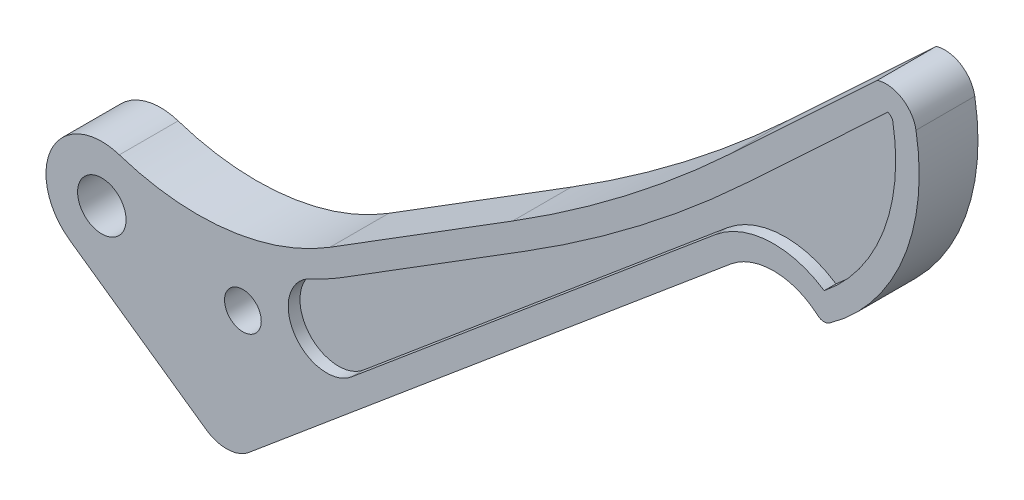
SolidWorks part; units mm, degrees
material "6061 Alloy"
ref_plane "Front Plane" through (0, 0, 0) normal (0, 0, 1) x (1, 0, 0)
ref_plane "Top Plane" through (0, 0, 0) normal (0, 1, 0) x (1, 0, 0)
ref_plane "Right Plane" through (0, 0, 0) normal (1, 0, 0) x (0, 0, -1)
sketch "Sketch1" plane through (0, 0, 0) normal (0, 0, 1) x (1, 0, 0)
  line L0 (36.4205, -14.9567) -> (38.1, -14.9567)
  line L1 (36.446, -14.812) -> (36.4205, -14.9567) construction
  line L2 (39.3098, -38.1358) -> (169.8026, 71.3084)
  line L3 (38.1, -5.4317) -> (37.2385, -10.3173) construction
  line L4 (38.1, -5.4317) -> (38.1, -27.0885) construction
  line L5 (28.2156, -38.2409) -> (-8.6667, -12.3423)
  line L6 (61.6023, 21.14) -> (110.9172, 51.9322)
  line L7 (209.4421, 134.1065) -> (169.8026, 97.1168)
  arc A0 (4.7355, 14.3185) -> (-8.6667, -12.3423) centre (0, 0) ccw
  arc A1 (36.446, -14.812) -> (38.1, -14.9567) centre (38.1, -5.4317) ccw
  arc A2 (28.2156, -38.2409) -> (39.3098, -38.1358) centre (33.6893, -30.4458) ccw
  arc A3 (4.7355, 14.3185) -> (61.6023, 21.14) centre (25.9011, 78.3167) ccw
  circle A4 centre (0, 0) radius 6.5484
  circle A5 centre (38.1, -5.4317) radius 4.9609
  arc A6 (219.8769, 127.6518) -> (196.5196, 70.8754) centre (163.3389, 117.7183) cw
  arc A7 (169.8026, 71.3084) -> (193.3752, 71.0397) centre (181.4324, 57.4421) cw
  arc A8 (219.8769, 127.6518) -> (209.4421, 134.1065) centre (211.7835, 126.2298) ccw
  arc A9 (196.5196, 70.8754) -> (193.3752, 71.0397) centre (195.0514, 72.9481) cw
  arc A10 (169.8026, 97.1168) -> (110.9172, 51.9322) centre (-93.4393, 379.2162) cw
  point P27 (63.0672, 19.894)
  point P28 (57.9017, 18.9895)
  point P30 (110.9172, 51.9322)
  point P31 (169.8026, 71.0397)
  dimension "D1" = 30.1625
  dimension "D2" = 19.05
  dimension "D6" = 19.05
  dimension "D14" = 13.0969
  dimension "D15" = 9.9219
  dimension "D16" = 5.4317
  dimension "D4" = 57.404
  dimension "D8" = 2.54
  dimension "D3" = 38.1
  dimension "D5" = 10
  dimension "D7" = 25.4
extrude "Boss-Extrude1" add sketch "Sketch1" along normal blind 15.875
ref_plane "Plane1" through (0, 0, 7.9375) normal (0, 0, 1) x (1, 0, 0)
sketch "Sketch2" plane through (0, 0, 0) normal (0, 0, -1) x (-1, 0, 0)
  line L12 (-174.1349, 92.4742) -> (-212.2471, 128.0387)
  line L13 (-165.7221, 76.1738) -> (-35.4353, -33.0976)
  line L14 (-31.8648, -33.0442) -> (5.0176, -7.1455)
  line L15 (-64.9655, 15.7537) -> (-114.2803, 46.546)
  line L16 (-174.1349, 92.4742) -> (-212.2471, 128.0387)
  line L17 (-165.7221, 76.1738) -> (-67.4276, -6.2657)
  line L19 (-64.9655, 15.7537) -> (-114.2803, 46.546)
  arc A19 (-51.1856, -2.4075) -> (-67.4276, -6.2657) centre (-60.7419, 1.7057) cw
  arc A22 (-56.4349, 11.1763) -> (-51.1856, -2.4075) centre (-60.7419, 1.7057) cw
  arc A26 (-212.2471, 128.0387) -> (-213.6227, 126.5529) centre (-211.7835, 126.2298) ccw
  arc A27 (-213.6227, 126.5529) -> (-195.0767, 77.7281) centre (-163.3389, 117.7183) ccw
  arc A28 (-165.7221, 76.1738) -> (-195.0767, 77.7281) centre (-181.4324, 57.4421) ccw
  arc A29 (-35.4353, -33.0976) -> (-31.8648, -33.0442) centre (-33.6893, -30.4458) ccw
  arc A30 (5.0176, -7.1455) -> (-2.7416, 8.2897) centre (0, 0) ccw
  arc A31 (-64.9655, 15.7537) -> (-2.7416, 8.2897) centre (-25.9011, 78.3167) ccw
  arc A32 (-174.1349, 92.4742) -> (-114.2803, 46.546) centre (93.4393, 379.2162) ccw
  arc A33 (-212.2471, 128.0387) -> (-213.6227, 126.5529) centre (-211.7835, 126.2298) ccw
  arc A34 (-213.6227, 126.5529) -> (-195.0767, 77.7281) centre (-163.3389, 117.7183) ccw
  arc A35 (-165.7221, 76.1738) -> (-195.0767, 77.7281) centre (-181.4324, 57.4421) ccw
  arc A38 (-64.9655, 15.7537) -> (-56.4349, 11.1763) centre (-25.9011, 78.3167) ccw
  arc A39 (-174.1349, 92.4742) -> (-114.2803, 46.546) centre (93.4393, 379.2162) ccw
  point P3 (0, 0)
  point P4 (0, 0)
  point P5 (-49.9071, -4.6152)
  point P6 (0, 0)
  point P9 (-60.7419, 1.7057)
  dimension "D1" = 6.35
extrude "Cut-Extrude1" cut sketch "Sketch2" against normal blind 3.175
ref_plane "Plane2" through (0, 0, 7.9375) normal (0, 0, -1) x (-1, 0, 0)
mirror "Mirror1" about plane through (0, 0, 7.9375) normal (0, 0, -1) of "Cut-Extrude1"
